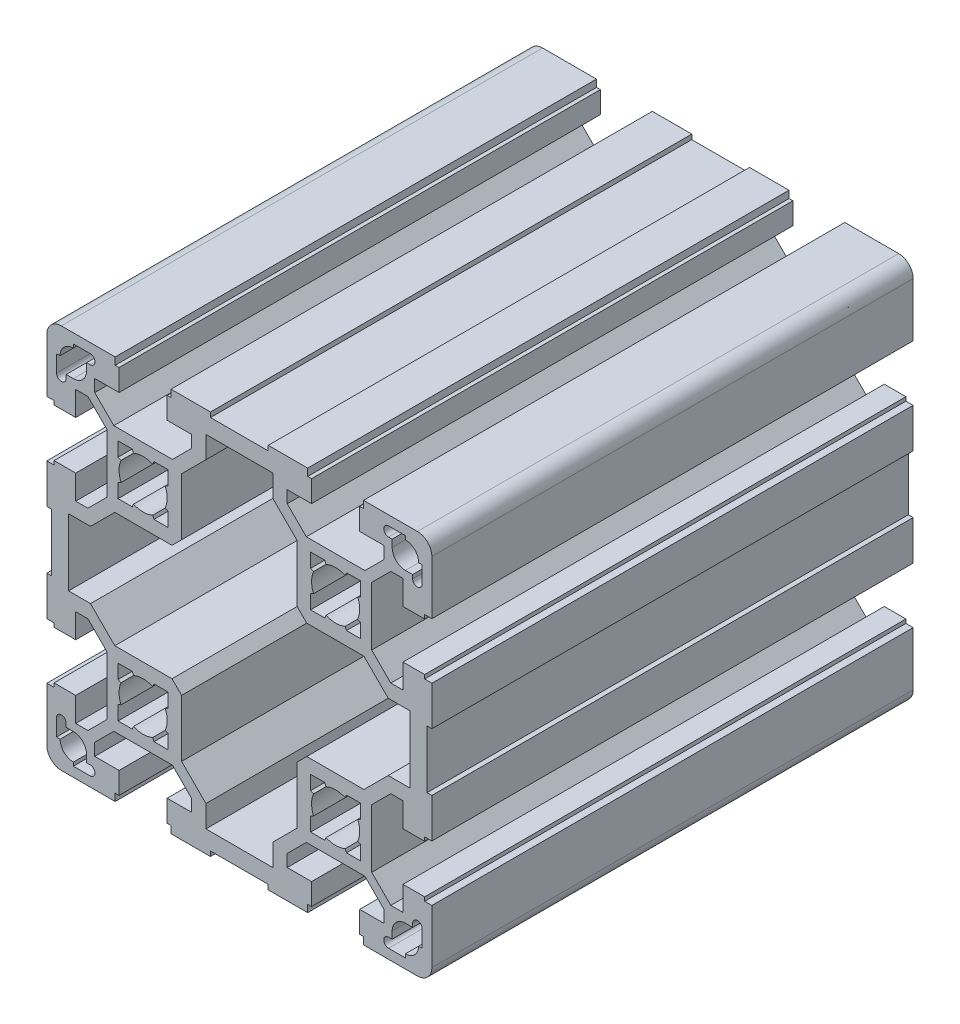
SolidWorks part; units mm, degrees
ref_plane "Front Plane" through (0, 0, 0) normal (0, 0, 1) x (1, 0, 0)
ref_plane "Top Plane" through (0, 0, 0) normal (0, 1, 0) x (1, 0, 0)
ref_plane "Right Plane" through (0, 0, 0) normal (1, 0, 0) x (0, 0, -1)
sketch "Sketch2" plane through (0, 0, 0) normal (0, 0, 1) x (1, 0, 0)
  line L0 (-55.3038, 0) -> (67.8331, 0) construction
  line L1 (0, 45.512) -> (0, -57.6815) construction
  line L2 (25.2, 17.739) -> (24.5853, 18.0063)
  line L3 (17.739, 25.2) -> (18.0063, 24.5853)
  line L4 (6, 40) -> (6, 39)
  line L5 (30.05, 34) -> (30.05, 31.4642)
  line L6 (38, 34.5) -> (37.25, 34.5)
  line L7 (39, -6) -> (39, 6)
  line L8 (35.5, -6.95) -> (35.5, 6.95)
  line L9 (26.0858, 27.5) -> (13.9142, 27.5)
  line L10 (-9.95, 31.4642) -> (-13.9142, 27.5)
  line L11 (-9.95, 34) -> (-9.95, 31.4642)
  line L12 (-15, 34) -> (-9.95, 34)
  line L13 (-15, 38.5) -> (-15, 34)
  line L14 (-15, 38.5) -> (-14.2, 38.5)
  line L15 (-14.2, 40) -> (-14.2, 38.5)
  line L16 (-14.2, 40) -> (-6, 40)
  line L17 (-6.95, 30.9287) -> (-6.95, 35.5)
  line L18 (-12, 25.8787) -> (-6.95, 30.9287)
  line L19 (-12, 14) -> (-12, 25.8787)
  line L20 (6, 39) -> (-6, 39)
  line L21 (30.05, 31.4642) -> (26.0858, 27.5)
  line L22 (6.95, 35.5) -> (-6.95, 35.5)
  line L23 (30.05, 34) -> (25, 34)
  line L24 (25, 34) -> (25, 38.5)
  line L25 (25.8, 38.5) -> (25, 38.5)
  line L26 (25.8, 38.5) -> (25.8, 40)
  line L27 (37, 40) -> (25.8, 40)
  line L28 (40, 37) -> (40, 25.8)
  line L29 (34.5, 37.25) -> (34.5, 38)
  line L30 (34.5, 38) -> (31, 38)
  line L31 (31.75, 36) -> (31, 36)
  line L32 (31.75, 36) -> (31.75, 34.5)
  line L33 (36, 31.75) -> (34.5, 31.75)
  line L34 (36, 31.75) -> (36, 31)
  line L35 (38, 31) -> (38, 34.5)
  line L36 (40, 25.8) -> (38.5, 25.8)
  line L37 (38.5, 25.8) -> (38.5, 25)
  line L38 (38.5, 25) -> (34, 25)
  line L39 (34, 25) -> (34, 30.05)
  line L40 (34, 30.05) -> (31.4642, 30.05)
  line L41 (31.4642, 30.05) -> (27.5, 26.0858)
  line L42 (25.2, 25.2) -> (22.261, 25.2)
  line L43 (17.739, 25.2) -> (14.8, 25.2)
  line L44 (14.8, 25.2) -> (14.8, 22.261)
  line L45 (25.2, 22.261) -> (25.2, 25.2)
  line L46 (22.261, 25.2) -> (21.9937, 24.5853)
  line L47 (25.2, 22.261) -> (24.5853, 21.9937)
  line L48 (14.8, 22.261) -> (15.4147, 21.9937)
  line L49 (15.4147, 18.0063) -> (14.8, 17.739)
  line L50 (14.8, 14.8) -> (14.8, 17.739)
  line L51 (17.739, 14.8) -> (14.8, 14.8)
  line L52 (17.739, 14.8) -> (18.0063, 15.4147)
  line L53 (22.261, 14.8) -> (21.9937, 15.4147)
  line L54 (25.2, 14.8) -> (22.261, 14.8)
  line L55 (25.2, 14.8) -> (25.2, 17.739)
  line L56 (27.5, 26.0858) -> (27.5, 13.9142)
  line L57 (31.4642, 9.95) -> (27.5, 13.9142)
  line L58 (34, 9.95) -> (31.4642, 9.95)
  line L59 (34, 9.95) -> (34, 15)
  line L60 (38.5, 15) -> (34, 15)
  line L61 (38.5, 14.2) -> (38.5, 15)
  line L62 (40, 14.2) -> (38.5, 14.2)
  line L63 (40, 6) -> (40, 14.2)
  line L64 (40, 6) -> (39, 6)
  line L65 (35.5, 6.95) -> (30.9287, 6.95)
  line L66 (30.9287, 6.95) -> (25.8787, 12)
  line L67 (25.8787, 12) -> (14, 12)
  line L68 (14, 12) -> (12, 14)
  line L69 (12, 14) -> (12, 25.8787)
  line L70 (12, 25.8787) -> (6.95, 30.9287)
  line L71 (6.95, 30.9287) -> (6.95, 35.5)
  line L72 (14.2, 40) -> (6, 40)
  line L73 (-14, 12) -> (-12, 14)
  line L74 (-25.8787, 12) -> (-14, 12)
  line L75 (-30.9287, 6.95) -> (-25.8787, 12)
  line L76 (-35.5, 6.95) -> (-30.9287, 6.95)
  line L77 (-40, 6) -> (-39, 6)
  line L78 (-40, 6) -> (-40, 14.2)
  line L79 (-40, 14.2) -> (-38.5, 14.2)
  line L80 (-38.5, 14.2) -> (-38.5, 15)
  line L81 (-38.5, 15) -> (-34, 15)
  line L82 (-34, 9.95) -> (-34, 15)
  line L83 (-34, 9.95) -> (-31.4642, 9.95)
  line L84 (-31.4642, 9.95) -> (-27.5, 13.9142)
  line L85 (-27.5, 26.0858) -> (-27.5, 13.9142)
  line L86 (-25.2, 14.8) -> (-25.2, 17.739)
  line L87 (-25.2, 14.8) -> (-22.261, 14.8)
  line L88 (-22.261, 14.8) -> (-21.9937, 15.4147)
  line L89 (-17.739, 14.8) -> (-18.0063, 15.4147)
  line L90 (-17.739, 14.8) -> (-14.8, 14.8)
  line L91 (-14.8, 14.8) -> (-14.8, 17.739)
  line L92 (-15.4147, 18.0063) -> (-14.8, 17.739)
  line L93 (-14.8, 22.261) -> (-15.4147, 21.9937)
  line L94 (-25.2, 22.261) -> (-24.5853, 21.9937)
  line L95 (-22.261, 25.2) -> (-21.9937, 24.5853)
  line L96 (-25.2, 22.261) -> (-25.2, 25.2)
  line L97 (-14.8, 25.2) -> (-14.8, 22.261)
  line L98 (-17.739, 25.2) -> (-14.8, 25.2)
  line L99 (-25.2, 25.2) -> (-22.261, 25.2)
  line L100 (-31.4642, 30.05) -> (-27.5, 26.0858)
  line L101 (-34, 30.05) -> (-31.4642, 30.05)
  line L102 (-34, 25) -> (-34, 30.05)
  line L103 (-38.5, 25) -> (-34, 25)
  line L104 (-38.5, 25.8) -> (-38.5, 25)
  line L105 (-40, 25.8) -> (-38.5, 25.8)
  line L106 (-38, 31) -> (-38, 34.5)
  line L107 (-36, 31.75) -> (-36, 31)
  line L108 (-36, 31.75) -> (-34.5, 31.75)
  line L109 (-31.75, 36) -> (-31.75, 34.5)
  line L110 (-31.75, 36) -> (-31, 36)
  line L111 (-34.5, 38) -> (-31, 38)
  line L112 (-34.5, 37.25) -> (-34.5, 38)
  line L113 (-40, 37) -> (-40, 25.8)
  line L114 (-37, 40) -> (-25.8, 40)
  line L115 (-25.8, 38.5) -> (-25.8, 40)
  line L116 (-25.8, 38.5) -> (-25, 38.5)
  line L117 (-25, 34) -> (-25, 38.5)
  line L118 (-30.05, 34) -> (-25, 34)
  line L119 (-30.05, 31.4642) -> (-26.0858, 27.5)
  line L120 (-26.0858, 27.5) -> (-13.9142, 27.5)
  line L121 (-35.5, -6.95) -> (-35.5, 6.95)
  line L122 (14.2, 40) -> (14.2, 38.5)
  line L123 (-39, -6) -> (-39, 6)
  line L124 (15, 38.5) -> (14.2, 38.5)
  line L125 (-38, 34.5) -> (-37.25, 34.5)
  line L126 (15, 38.5) -> (15, 34)
  line L127 (15, 34) -> (9.95, 34)
  line L128 (9.95, 34) -> (9.95, 31.4642)
  line L129 (9.95, 31.4642) -> (13.9142, 27.5)
  line L130 (-25.2, -17.739) -> (-24.5853, -18.0063)
  line L131 (-17.739, -25.2) -> (-18.0063, -24.5853)
  line L132 (-6, -40) -> (-6, -39)
  line L133 (-30.05, -34) -> (-30.05, -31.4642)
  line L134 (9.95, -31.4642) -> (13.9142, -27.5)
  line L135 (9.95, -34) -> (9.95, -31.4642)
  line L136 (15, -34) -> (9.95, -34)
  line L137 (15, -38.5) -> (15, -34)
  line L138 (-38, -34.5) -> (-37.25, -34.5)
  line L139 (15, -38.5) -> (14.2, -38.5)
  line L140 (14.2, -40) -> (14.2, -38.5)
  line L141 (-26.0858, -27.5) -> (-13.9142, -27.5)
  line L142 (-30.05, -31.4642) -> (-26.0858, -27.5)
  line L143 (-30.05, -34) -> (-25, -34)
  line L144 (-25, -34) -> (-25, -38.5)
  line L145 (-25.8, -38.5) -> (-25, -38.5)
  line L146 (-25.8, -38.5) -> (-25.8, -40)
  line L147 (-37, -40) -> (-25.8, -40)
  line L148 (-40, -37) -> (-40, -25.8)
  line L149 (-34.5, -37.25) -> (-34.5, -38)
  line L150 (-34.5, -38) -> (-31, -38)
  line L151 (-31.75, -36) -> (-31, -36)
  line L152 (-31.75, -36) -> (-31.75, -34.5)
  line L153 (-36, -31.75) -> (-34.5, -31.75)
  line L154 (-36, -31.75) -> (-36, -31)
  line L155 (-38, -31) -> (-38, -34.5)
  line L156 (-40, -25.8) -> (-38.5, -25.8)
  line L157 (-38.5, -25.8) -> (-38.5, -25)
  line L158 (-38.5, -25) -> (-34, -25)
  line L159 (-34, -25) -> (-34, -30.05)
  line L160 (-34, -30.05) -> (-31.4642, -30.05)
  line L161 (-31.4642, -30.05) -> (-27.5, -26.0858)
  line L162 (-25.2, -25.2) -> (-22.261, -25.2)
  line L163 (-17.739, -25.2) -> (-14.8, -25.2)
  line L164 (-14.8, -25.2) -> (-14.8, -22.261)
  line L165 (-25.2, -22.261) -> (-25.2, -25.2)
  line L166 (-22.261, -25.2) -> (-21.9937, -24.5853)
  line L167 (-25.2, -22.261) -> (-24.5853, -21.9937)
  line L168 (-14.8, -22.261) -> (-15.4147, -21.9937)
  line L169 (-15.4147, -18.0063) -> (-14.8, -17.739)
  line L170 (-14.8, -14.8) -> (-14.8, -17.739)
  line L171 (-17.739, -14.8) -> (-14.8, -14.8)
  line L172 (-17.739, -14.8) -> (-18.0063, -15.4147)
  line L173 (-22.261, -14.8) -> (-21.9937, -15.4147)
  line L174 (-25.2, -14.8) -> (-22.261, -14.8)
  line L175 (-25.2, -14.8) -> (-25.2, -17.739)
  line L176 (-27.5, -26.0858) -> (-27.5, -13.9142)
  line L177 (-31.4642, -9.95) -> (-27.5, -13.9142)
  line L178 (-34, -9.95) -> (-31.4642, -9.95)
  line L179 (-34, -9.95) -> (-34, -15)
  line L180 (-38.5, -15) -> (-34, -15)
  line L181 (-38.5, -14.2) -> (-38.5, -15)
  line L182 (-40, -14.2) -> (-38.5, -14.2)
  line L183 (-40, -6) -> (-40, -14.2)
  line L184 (-40, -6) -> (-39, -6)
  line L185 (-35.5, -6.95) -> (-30.9287, -6.95)
  line L186 (-30.05, 34) -> (-30.05, 31.4642)
  line L187 (-6, 40) -> (-6, 39)
  line L188 (-30.9287, -6.95) -> (-25.8787, -12)
  line L189 (-25.8787, -12) -> (-14, -12)
  line L190 (-14, -12) -> (-12, -14)
  line L191 (14.2, -40) -> (6, -40)
  line L192 (6.95, -30.9287) -> (6.95, -35.5)
  line L193 (12, -25.8787) -> (6.95, -30.9287)
  line L194 (12, -14) -> (12, -25.8787)
  line L195 (14, -12) -> (12, -14)
  line L196 (25.8787, -12) -> (14, -12)
  line L197 (30.9287, -6.95) -> (25.8787, -12)
  line L198 (35.5, -6.95) -> (30.9287, -6.95)
  line L199 (40, -6) -> (39, -6)
  line L200 (40, -6) -> (40, -14.2)
  line L201 (40, -14.2) -> (38.5, -14.2)
  line L202 (38.5, -14.2) -> (38.5, -15)
  line L203 (38.5, -15) -> (34, -15)
  line L204 (34, -9.95) -> (34, -15)
  line L205 (34, -9.95) -> (31.4642, -9.95)
  line L206 (31.4642, -9.95) -> (27.5, -13.9142)
  line L207 (27.5, -26.0858) -> (27.5, -13.9142)
  line L208 (25.2, -14.8) -> (25.2, -17.739)
  line L209 (25.2, -14.8) -> (22.261, -14.8)
  line L210 (22.261, -14.8) -> (21.9937, -15.4147)
  line L211 (17.739, -14.8) -> (18.0063, -15.4147)
  line L212 (17.739, -14.8) -> (14.8, -14.8)
  line L213 (14.8, -14.8) -> (14.8, -17.739)
  line L214 (15.4147, -18.0063) -> (14.8, -17.739)
  line L215 (14.8, -22.261) -> (15.4147, -21.9937)
  line L216 (25.2, -22.261) -> (24.5853, -21.9937)
  line L217 (22.261, -25.2) -> (21.9937, -24.5853)
  line L218 (25.2, -22.261) -> (25.2, -25.2)
  line L219 (14.8, -25.2) -> (14.8, -22.261)
  line L220 (17.739, -25.2) -> (14.8, -25.2)
  line L221 (25.2, -25.2) -> (22.261, -25.2)
  line L222 (31.4642, -30.05) -> (27.5, -26.0858)
  line L223 (34, -30.05) -> (31.4642, -30.05)
  line L224 (34, -25) -> (34, -30.05)
  line L225 (38.5, -25) -> (34, -25)
  line L226 (38.5, -25.8) -> (38.5, -25)
  line L227 (40, -25.8) -> (38.5, -25.8)
  line L228 (38, -31) -> (38, -34.5)
  line L229 (36, -31.75) -> (36, -31)
  line L230 (36, -31.75) -> (34.5, -31.75)
  line L231 (31.75, -36) -> (31.75, -34.5)
  line L232 (31.75, -36) -> (31, -36)
  line L233 (34.5, -38) -> (31, -38)
  line L234 (34.5, -37.25) -> (34.5, -38)
  line L235 (40, -37) -> (40, -25.8)
  line L236 (37, -40) -> (25.8, -40)
  line L237 (25.8, -38.5) -> (25.8, -40)
  line L238 (25.8, -38.5) -> (25, -38.5)
  line L239 (25, -34) -> (25, -38.5)
  line L240 (30.05, -34) -> (25, -34)
  line L241 (6.95, -35.5) -> (-6.95, -35.5)
  line L242 (30.05, -31.4642) -> (26.0858, -27.5)
  line L243 (6, -39) -> (-6, -39)
  line L244 (-12, -14) -> (-12, -25.8787)
  line L245 (-12, -25.8787) -> (-6.95, -30.9287)
  line L246 (-6.95, -30.9287) -> (-6.95, -35.5)
  line L247 (-14.2, -40) -> (-6, -40)
  line L248 (-14.2, -40) -> (-14.2, -38.5)
  line L249 (-15, -38.5) -> (-14.2, -38.5)
  line L250 (-15, -38.5) -> (-15, -34)
  line L251 (-15, -34) -> (-9.95, -34)
  line L252 (-9.95, -34) -> (-9.95, -31.4642)
  line L253 (-9.95, -31.4642) -> (-13.9142, -27.5)
  line L254 (26.0858, -27.5) -> (13.9142, -27.5)
  line L255 (38, -34.5) -> (37.25, -34.5)
  line L256 (30.05, -34) -> (30.05, -31.4642)
  line L257 (6, -40) -> (6, -39)
  line L258 (17.739, -25.2) -> (18.0063, -24.5853)
  line L259 (25.2, -17.739) -> (24.5853, -18.0063)
  line L306 (-17.739, 25.2) -> (-18.0063, 24.5853)
  line L307 (-25.2, 17.739) -> (-24.5853, 18.0063)
  arc A0 (37, 40) -> (40, 37) centre (37, 37) cw
  arc A1 (34.5, 37.25) -> (37.25, 34.5) centre (34.5, 34.5) cw
  arc A2 (31, 36) -> (31, 38) centre (31, 37) cw
  arc A3 (34.5, 31.75) -> (31.75, 34.5) centre (34.5, 34.5) cw
  arc A4 (38, 31) -> (36, 31) centre (37, 31) cw
  arc A5 (18.0063, 24.5853) -> (21.9937, 24.5853) centre (20, 20) cw
  arc A6 (24.5853, 21.9937) -> (24.5853, 18.0063) centre (20, 20) cw
  arc A7 (15.4147, 18.0063) -> (15.4147, 21.9937) centre (20, 20) cw
  arc A8 (21.9937, 15.4147) -> (18.0063, 15.4147) centre (20, 20) cw
  arc A9 (-21.9937, 15.4147) -> (-18.0063, 15.4147) centre (-20, 20) ccw
  arc A10 (-15.4147, 18.0063) -> (-15.4147, 21.9937) centre (-20, 20) ccw
  arc A11 (-24.5853, 21.9937) -> (-24.5853, 18.0063) centre (-20, 20) ccw
  arc A12 (-18.0063, 24.5853) -> (-21.9937, 24.5853) centre (-20, 20) ccw
  arc A13 (-38, 31) -> (-36, 31) centre (-37, 31) ccw
  arc A14 (-34.5, 31.75) -> (-31.75, 34.5) centre (-34.5, 34.5) ccw
  arc A15 (-31, 36) -> (-31, 38) centre (-31, 37) ccw
  arc A16 (-34.5, 37.25) -> (-37.25, 34.5) centre (-34.5, 34.5) ccw
  arc A17 (-37, 40) -> (-40, 37) centre (-37, 37) ccw
  arc A18 (-37, -40) -> (-40, -37) centre (-37, -37) cw
  arc A19 (-34.5, -37.25) -> (-37.25, -34.5) centre (-34.5, -34.5) cw
  arc A20 (-31, -36) -> (-31, -38) centre (-31, -37) cw
  arc A21 (-34.5, -31.75) -> (-31.75, -34.5) centre (-34.5, -34.5) cw
  arc A22 (-38, -31) -> (-36, -31) centre (-37, -31) cw
  arc A23 (-18.0063, -24.5853) -> (-21.9937, -24.5853) centre (-20, -20) cw
  arc A24 (-24.5853, -21.9937) -> (-24.5853, -18.0063) centre (-20, -20) cw
  arc A25 (-15.4147, -18.0063) -> (-15.4147, -21.9937) centre (-20, -20) cw
  arc A26 (-21.9937, -15.4147) -> (-18.0063, -15.4147) centre (-20, -20) cw
  arc A27 (21.9937, -15.4147) -> (18.0063, -15.4147) centre (20, -20) ccw
  arc A28 (15.4147, -18.0063) -> (15.4147, -21.9937) centre (20, -20) ccw
  arc A29 (24.5853, -21.9937) -> (24.5853, -18.0063) centre (20, -20) ccw
  arc A30 (18.0063, -24.5853) -> (21.9937, -24.5853) centre (20, -20) ccw
  arc A31 (38, -31) -> (36, -31) centre (37, -31) ccw
  arc A32 (34.5, -31.75) -> (31.75, -34.5) centre (34.5, -34.5) ccw
  arc A33 (31, -36) -> (31, -38) centre (31, -37) ccw
  arc A34 (34.5, -37.25) -> (37.25, -34.5) centre (34.5, -34.5) ccw
  arc A35 (37, -40) -> (40, -37) centre (37, -37) ccw
  point P22 (0, 39)
  point P110 (35.5, 0)
  point P111 (39, 0)
  point P121 (39, 0)
  point P162 (0, 35.5)
  point P165 (0, 35.5)
  point P166 (0, 39)
  point P218 (0, -39)
  point P219 (0, -35.5)
  point P234 (-39, 0)
  point P236 (-35.5, 0)
  point P279 (-39, 0)
  point P280 (-35.5, 0)
  point P334 (35.5, 0)
  dimension "D4" = 10
  dimension "D1" = 10
  dimension "D2" = 80
  dimension "D3" = 80
extrude "Base-Extrude" add sketch "Sketch2" against normal blind 100
